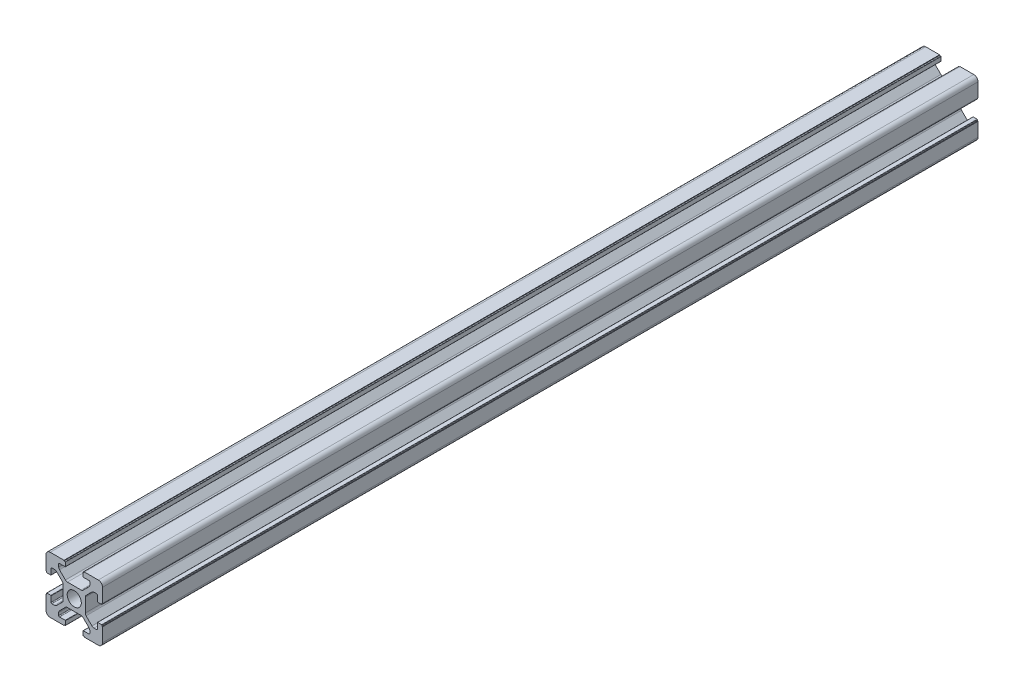
SolidWorks part; units mm, degrees
material "6063-T5"
ref_plane "前视基准面" through (0, 0, 0) normal (0, 0, 1) x (1, 0, 0)
ref_plane "上视基准面" through (0, 0, 0) normal (0, 1, 0) x (1, 0, 0)
ref_plane "右视基准面" through (0, 0, 0) normal (1, 0, 0) x (0, 0, -1)
sketch "草图1" plane through (0, 0, 0) normal (0, 0, 1) x (1, 0, 0)
  line L0 (-1.4389, 10) -> (24.3741, 10) construction
  line L1 (20, 13.6) -> (20, 20)
  line L2 (0, 0) -> (0, 6.4)
  line L3 (0, 20) -> (6.4, 20)
  line L4 (20, 0) -> (20, 6.4)
  line L5 (10, 21.5388) -> (10, -2.4017) construction
  line L6 (6.9, 18.3) -> (6.9, 19.7)
  line L7 (6.8, 18.2) -> (4.8, 18.2)
  line L8 (4.5, 17.9) -> (4.5, 16.9749)
  line L9 (4.7929, 16.2678) -> (6.8678, 14.1929)
  line L10 (7.5749, 13.9) -> (12.4251, 13.9)
  line L11 (6.8, 19.8) -> (6.4, 19.8)
  line L12 (6.4, 19.8) -> (6.4, 20)
  line L13 (0, 13.6) -> (0.2, 13.6)
  line L14 (0.2, 13.6) -> (0.2, 13.2)
  line L15 (0.3, 13.1) -> (1.7, 13.1)
  line L16 (1.8, 13.2) -> (1.8, 15.2)
  line L17 (2.1, 15.5) -> (3.0251, 15.5)
  line L18 (3.7322, 15.2071) -> (5.8071, 13.1322)
  line L19 (6.1, 12.4251) -> (6.1, 7.5749)
  line L20 (13.6, 19.8) -> (13.6, 20)
  line L21 (13.2, 19.8) -> (13.6, 19.8)
  line L22 (13.1, 18.3) -> (13.1, 19.7)
  line L23 (13.2, 18.2) -> (15.2, 18.2)
  line L24 (15.5, 17.9) -> (15.5, 16.9749)
  line L25 (15.2071, 16.2678) -> (13.1322, 14.1929)
  line L26 (0, 6.4) -> (0.2, 6.4)
  line L27 (0.2, 6.4) -> (0.2, 6.8)
  line L28 (0.3, 6.9) -> (1.7, 6.9)
  line L29 (1.8, 6.8) -> (1.8, 4.8)
  line L30 (2.1, 4.5) -> (3.0251, 4.5)
  line L31 (3.7322, 4.7929) -> (5.8071, 6.8678)
  line L32 (13.6, 20) -> (20, 20)
  line L33 (0, 13.6) -> (0, 20)
  line L34 (13.6, 0.2) -> (13.6, 0)
  line L35 (13.2, 0.2) -> (13.6, 0.2)
  line L36 (13.1, 1.7) -> (13.1, 0.3)
  line L37 (13.2, 1.8) -> (15.2, 1.8)
  line L38 (15.5, 2.1) -> (15.5, 3.0251)
  line L39 (15.2071, 3.7322) -> (13.1322, 5.8071)
  line L40 (4.5, 2.1) -> (4.5, 3.0251)
  line L41 (6.8, 1.8) -> (4.8, 1.8)
  line L42 (6.4, 0.2) -> (6.4, 0)
  line L43 (6.8, 0.2) -> (6.4, 0.2)
  line L44 (6.9, 1.7) -> (6.9, 0.3)
  line L45 (4.7929, 3.7322) -> (6.8678, 5.8071)
  line L46 (7.5749, 6.1) -> (12.4251, 6.1)
  line L47 (20, 6.4) -> (19.8, 6.4)
  line L48 (19.8, 6.4) -> (19.8, 6.8)
  line L49 (19.7, 6.9) -> (18.3, 6.9)
  line L50 (18.2, 6.8) -> (18.2, 4.8)
  line L51 (17.9, 4.5) -> (16.9749, 4.5)
  line L52 (16.2678, 4.7929) -> (14.1929, 6.8678)
  line L53 (13.9, 12.4251) -> (13.9, 7.5749)
  line L54 (16.2678, 15.2071) -> (14.1929, 13.1322)
  line L55 (17.9, 15.5) -> (16.9749, 15.5)
  line L56 (18.2, 13.2) -> (18.2, 15.2)
  line L57 (19.7, 13.1) -> (18.3, 13.1)
  line L58 (19.8, 13.6) -> (19.8, 13.2)
  line L59 (20, 13.6) -> (19.8, 13.6)
  line L60 (0, 0) -> (6.4, 0)
  line L61 (13.6, 0) -> (20, 0)
  arc A0 (6.1, 12.4251) -> (5.8071, 13.1322) centre (5.1, 12.4251) ccw
  arc A1 (7.5749, 13.9) -> (6.8678, 14.1929) centre (7.5749, 14.9) cw
  arc A2 (4.5, 16.9749) -> (4.7929, 16.2678) centre (5.5, 16.9749) ccw
  arc A3 (3.7322, 15.2071) -> (3.0251, 15.5) centre (3.0251, 14.5) ccw
  arc A4 (4.5, 17.9) -> (4.8, 18.2) centre (4.8, 17.9) cw
  arc A5 (1.8, 15.2) -> (2.1, 15.5) centre (2.1, 15.2) cw
  arc A6 (0.3, 13.1) -> (0.2, 13.2) centre (0.3, 13.2) cw
  arc A7 (6.9, 19.7) -> (6.8, 19.8) centre (6.8, 19.7) ccw
  arc A8 (1.7, 13.1) -> (1.8, 13.2) centre (1.7, 13.2) ccw
  arc A9 (6.9, 18.3) -> (6.8, 18.2) centre (6.8, 18.3) cw
  arc A10 (13.1, 19.7) -> (13.2, 19.8) centre (13.2, 19.7) cw
  arc A11 (13.1, 18.3) -> (13.2, 18.2) centre (13.2, 18.3) ccw
  arc A12 (15.5, 17.9) -> (15.2, 18.2) centre (15.2, 17.9) ccw
  arc A13 (15.5, 16.9749) -> (15.2071, 16.2678) centre (14.5, 16.9749) cw
  arc A14 (12.4251, 13.9) -> (13.1322, 14.1929) centre (12.4251, 14.9) ccw
  arc A15 (0.3, 6.9) -> (0.2, 6.8) centre (0.3, 6.8) ccw
  arc A16 (1.7, 6.9) -> (1.8, 6.8) centre (1.7, 6.8) cw
  arc A17 (1.8, 4.8) -> (2.1, 4.5) centre (2.1, 4.8) ccw
  arc A18 (3.7322, 4.7929) -> (3.0251, 4.5) centre (3.0251, 5.5) cw
  arc A19 (6.1, 7.5749) -> (5.8071, 6.8678) centre (5.1, 7.5749) cw
  arc A20 (13.1, 0.3) -> (13.2, 0.2) centre (13.2, 0.3) ccw
  arc A21 (13.1, 1.7) -> (13.2, 1.8) centre (13.2, 1.7) cw
  arc A22 (15.5, 2.1) -> (15.2, 1.8) centre (15.2, 2.1) cw
  arc A23 (15.5, 3.0251) -> (15.2071, 3.7322) centre (14.5, 3.0251) ccw
  arc A24 (12.4251, 6.1) -> (13.1322, 5.8071) centre (12.4251, 5.1) cw
  arc A25 (4.5, 2.1) -> (4.8, 1.8) centre (4.8, 2.1) ccw
  arc A26 (6.9, 0.3) -> (6.8, 0.2) centre (6.8, 0.3) cw
  arc A27 (6.9, 1.7) -> (6.8, 1.8) centre (6.8, 1.7) ccw
  arc A28 (4.5, 3.0251) -> (4.7929, 3.7322) centre (5.5, 3.0251) cw
  arc A29 (7.5749, 6.1) -> (6.8678, 5.8071) centre (7.5749, 5.1) ccw
  arc A30 (19.7, 6.9) -> (19.8, 6.8) centre (19.7, 6.8) cw
  arc A31 (18.3, 6.9) -> (18.2, 6.8) centre (18.3, 6.8) ccw
  arc A32 (18.2, 4.8) -> (17.9, 4.5) centre (17.9, 4.8) cw
  arc A33 (16.2678, 4.7929) -> (16.9749, 4.5) centre (16.9749, 5.5) ccw
  arc A34 (13.9, 7.5749) -> (14.1929, 6.8678) centre (14.9, 7.5749) ccw
  arc A35 (13.9, 12.4251) -> (14.1929, 13.1322) centre (14.9, 12.4251) cw
  arc A36 (16.2678, 15.2071) -> (16.9749, 15.5) centre (16.9749, 14.5) cw
  arc A37 (18.2, 15.2) -> (17.9, 15.5) centre (17.9, 15.2) ccw
  arc A38 (18.3, 13.1) -> (18.2, 13.2) centre (18.3, 13.2) cw
  arc A39 (19.7, 13.1) -> (19.8, 13.2) centre (19.7, 13.2) ccw
  circle A40 centre (10, 10) radius 2.5
  point P39 (0.2, 13.1)
  point P42 (6.9, 19.8)
  point P45 (1.8, 13.1)
  point P48 (6.9, 18.2)
  point P66 (10, 13.9)
  point P83 (6.1, 10)
  dimension "D19" = 1
  dimension "D20" = 1
  dimension "D21" = 0.3
  dimension "D22" = 0.1
  dimension "D23" = 5
  dimension "D1" = 20
  dimension "D2" = 20
  dimension "D3" = 10
  dimension "D4" = 10
  dimension "D5" = 1.8
  dimension "D6" = 0.5
  dimension "D7" = 1.6
  dimension "D8" = 3.1
  dimension "D9" = 6.1
  dimension "D10" = 5.5
  dimension "D11" = 3.1
  dimension "D12" = 6.1
  dimension "D13" = 5.5
  dimension "D14" = 1.8
  dimension "D15" = 0.5
  dimension "D16" = 1.5
  dimension "D17" = 45
  dimension "D18" = 1.6
extrude "凸台-拉伸1" add sketch "草图1" along normal blind 310
fillet "圆角1" radius 1.5 4 edges at (20, 0, 155) (0, 0, 155) (0, 20, 155) (20, 20, 155)
